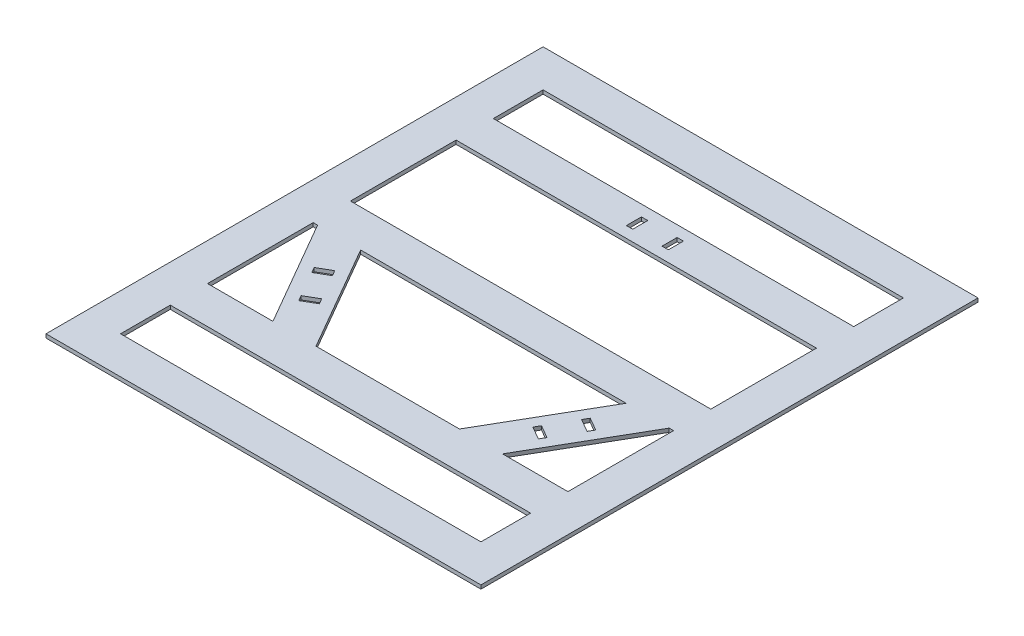
SolidWorks part; units mm, degrees
ref_plane "Alzado" through (0, 0, 0) normal (0, 0, 1) x (1, 0, 0)
ref_plane "Planta" through (0, 0, 0) normal (0, 1, 0) x (1, 0, 0)
ref_plane "Vista lateral" through (0, 0, 0) normal (1, 0, 0) x (0, 0, -1)
sketch "Croquis1" plane through (0, 0, 0) normal (0, 1, 0) x (1, 0, 0)
  line L0 (0, 0) -> (0, 115) construction
  line L1 (0, 0) -> (99.5929, -57.5) construction
  line L2 (-72.1688, 125) -> (-144.3376, 0) construction
  line L3 (-144.3376, 0) -> (-72.1688, -125) construction
  line L4 (-72.1688, -125) -> (72.1688, -125) construction
  line L5 (72.1688, -125) -> (144.3376, 0) construction
  line L6 (144.3376, 0) -> (72.1688, 125) construction
  line L7 (72.1688, 125) -> (-72.1688, 125) construction
  line L8 (-175, -200) -> (175, -200)
  line L9 (-175, -200) -> (-175, 200)
  line L10 (-175, 200) -> (175, 200)
  line L11 (175, -200) -> (175, 200)
  line L12 (-175, -200) -> (175, 200) construction
  line L13 (-175, 200) -> (175, -200) construction
  line L14 (0, 0) -> (-99.5929, -57.5) construction
  line L15 (-145, -170) -> (-145, 170)
  line L16 (-145, 170) -> (145, 170)
  line L17 (145, -170) -> (145, 170)
  line L18 (-145, -170) -> (145, -170)
  line L19 (-1000, 0) -> (49000, 0) construction
  line L20 (-145, 15) -> (145, 15)
  line L21 (-145, -15) -> (145, -15)
  line L22 (-1000, 115) -> (49000, 115) construction
  line L23 (-145, 130) -> (145, 130)
  line L24 (-145, 100) -> (145, 100)
  line L25 (-145, -100) -> (145, -100)
  line L26 (-145, -130) -> (145, -130)
  line L27 (-106.8098, -15) -> (-57.735, -100)
  line L28 (0, -1000) -> (0, 49000) construction
  line L29 (-141.4508, -15) -> (-92.376, -100)
  line L30 (141.4508, -15) -> (92.376, -100)
  line L31 (106.8098, -15) -> (57.735, -100)
  circle A0 centre (0, 0) radius 125 construction
  point P18 (0, 0)
  dimension "D2" = 250
  dimension "D1" = 115
  dimension "D3" = 400
  dimension "D4" = 350
  dimension "D7" = 30
  dimension "D8" = 30
  dimension "D9" = 30
  dimension "D10" = 15
  dimension "D6" = 30
  dimension "D5" = 3
extrude "Saliente-Extruir1" add sketch "Croquis1" along normal blind 3 contours L8 L11 L10 L9 L18 L15 L16 L17 | L15 L24 L17 L23 | L15 L21 L17 L20 | L15 L26 L17 L25 | L21 L29 L25 L27 | L21 L31 L25 L30
sketch "Croquis3" [suppressed] plane through (0, 0, 0) normal (1, 0, 0) x (0, 0, -1)
  line L0 (0, 0) -> (115, 0) construction
  line L1 (115, 0) -> (115, -15) construction
  line L2 (109, -15) -> (109, 0)
  line L3 (109, 0) -> (121, 0)
  line L4 (0, 0) -> (125, 0) construction
  line L5 (121, 0) -> (121, -15)
  arc A0 (109, -15) -> (121, -15) centre (115, -15) ccw
  circle A2 centre (115, -15) radius 1.6
  dimension "D3" = 12
  dimension "D4" = 3.2
  dimension "D1" = 115
  dimension "D2" = 15
extrude "Saliente-Extruir2" [suppressed] add sketch "Croquis3" along normal mid plane 30
sketch "Croquis4" [suppressed] plane through (0, 0, 0) normal (0, 0, 1) x (1, 0, 0)
  line L0 (-15, -21) -> (15, -21) construction
  line L1 (-10, 0) -> (10, 0)
  line L2 (-10, 0) -> (-10, -21)
  line L3 (-10, -21) -> (10, -21)
  line L4 (10, 0) -> (10, -21)
  dimension "D1" = 20
extrude "Cortar-Extruir1" [suppressed] cut sketch "Croquis4" against normal through all
sketch "Croquis5" [suppressed] plane through (0, 0, 0) normal (1, 0, 0) x (0, 0, -1)
  circle A0 centre (115, -15) radius 2.5
  circle A1 centre (115, -15) radius 1.6
  circle A2 centre (115, -15) radius 1.6 construction
  dimension "D1" = 5
extrude "Saliente-Extruir3" [suppressed] add sketch "Croquis5" along normal up to next and the other way up to next
sketch "Croquis6" [suppressed] plane through (0, 0, 0) normal (0, 0, 1) x (1, 0, 0)
  line L0 (10, -21) -> (15, -21) construction
  line L1 (-3, 0) -> (3, 0)
  line L2 (-3, 0) -> (-3, -21)
  line L3 (-3, -21) -> (3, -21)
  line L4 (3, 0) -> (3, -21)
  dimension "D1" = 6
extrude "Cortar-Extruir2" [suppressed] cut sketch "Croquis6" against normal through all
sketch "Croquis7" plane through (0, 0, 0) normal (1, 0, 0) x (0, 0, -1)
  line L0 (0, -1000) -> (0, 49000) construction
sketch "Croquis9" plane through (0, 0, 0) normal (0, 1, 0) x (1, 0, 0)
  line L0 (0, 0) -> (0, 115) construction
  line L1 (-11.8, 108.95) -> (-11.8, 121.05)
  line L2 (-16.9, 121.05) -> (16.9, 121.05)
  line L3 (-16.9, 121.05) -> (-16.9, 108.95)
  line L4 (-16.9, 108.95) -> (16.9, 108.95)
  line L5 (16.9, 121.05) -> (16.9, 108.95)
  line L6 (-16.9, 121.05) -> (16.9, 108.95) construction
  line L7 (-16.9, 108.95) -> (16.9, 121.05) construction
  line L8 (11.8, 108.95) -> (11.8, 121.05)
  dimension "D1" = 115
  dimension "D2" = 33.8
  dimension "D3" = 12.1
  dimension "D4" = 5.1
  dimension "D5" = 5.1
extrude "Cortar-Extruir3" cut sketch "Croquis9" along normal through all contours L3 L4 L1 L2 | L8 L4 L5 L2
pattern_circular "MatrizC2" count 3 over 360 about axis through (0, 0, 0) along (0, 1, 0) of "Cortar-Extruir3"
